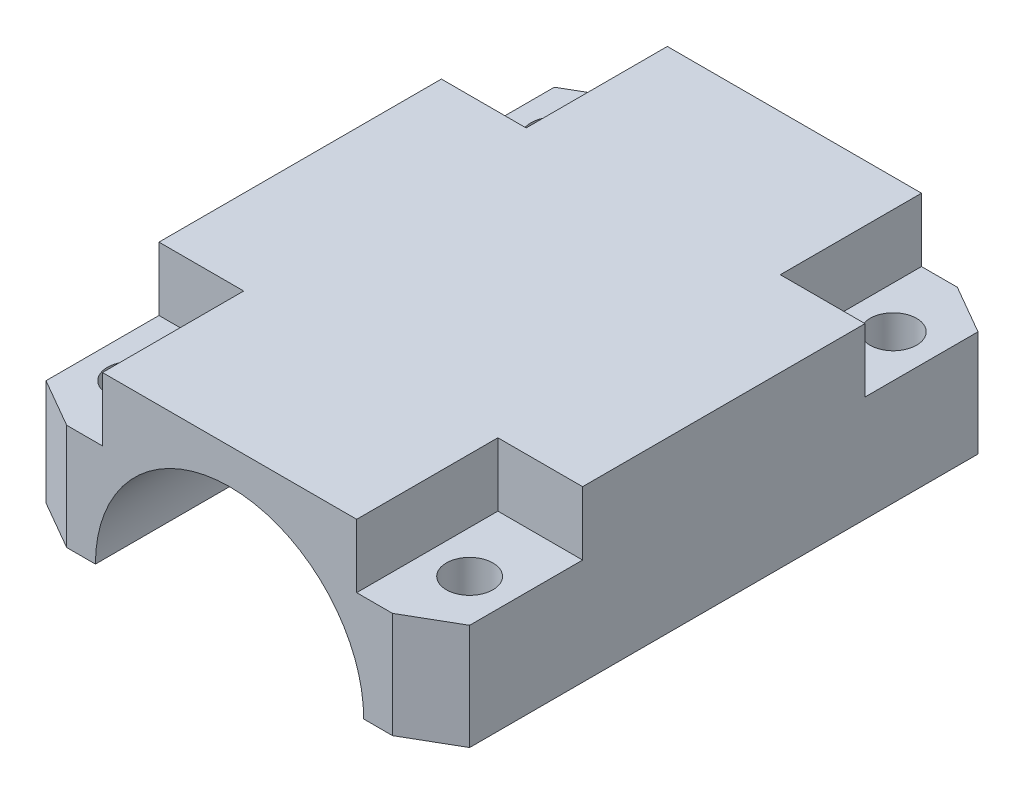
SolidWorks part; units mm, degrees
ref_plane "Plano frontal" through (0, 0, 0) normal (0, 0, 1) x (1, 0, 0)
ref_plane "Plano superior" through (0, 0, 0) normal (0, 1, 0) x (1, 0, 0)
ref_plane "Plano direito" through (0, 0, 0) normal (1, 0, 0) x (0, 0, -1)
sketch "Esboço1" plane through (0, 0, 0) normal (0, 1, 0) x (1, 0, 0)
  line L1 (0, 0) -> (-30, 0)
  line L2 (0, 0) -> (0, 40)
  line L3 (0, 40) -> (-30, 40)
  line L4 (-30, 0) -> (-30, 40)
  dimension "D1" = 30
  dimension "D2" = 40
extrude "Ressalto-extrusão1" add sketch "Esboço1" along normal blind 12
sketch "Esboço16" plane through (0, 0, 0) normal (0, -1, 0) x (1, 0, 0)
  line L1 (0, -40) -> (-30, -40) construction
  line L2 (-30, 0) -> (0, 0) construction
  line L4 (-15, -40) -> (-24.5, -40)
  line L5 (-15, -40) -> (-15, 0)
  line L6 (-15, 0) -> (-24.5, 0)
  line L7 (-24.5, -40) -> (-24.5, 0)
  point P1 (-15, -40)
  dimension "D1" = 9.5
revolve "Corte-Revolução1" cut sketch "Esboço16" angle 360 about L5
sketch "Esboço17" plane through (0, 0, 0) normal (0, -1, 0) x (1, 0, 0)
  line L0 (-23, -4) -> (-23, -36) construction
  line L1 (-27, -35) -> (-3, -35) construction
  line L2 (-27, -35) -> (-27, -5) construction
  line L3 (-27, -5) -> (-3, -5) construction
  line L4 (-3, -35) -> (-3, -5) construction
  line L5 (-5, 0) -> (-25, 0) construction
  line L6 (-30, -40) -> (-30, 0) construction
  line L8 (-24.5, -40) -> (-30, -40) construction
  circle A0 centre (-27, -35) radius 1.65
  circle A1 centre (-27, -5) radius 1.65
  circle A2 centre (-3, -35) radius 1.65
  circle A3 centre (-3, -5) radius 1.65
  point P8 (-27, -20)
  point P11 (-23, -20)
  point P12 (-15, -5)
  point P15 (-15, 0)
  dimension "D1" = 3.3
  dimension "D2" = 3
  dimension "D3" = 5
extrude "Corte-extrusão12" cut sketch "Esboço17" against normal through all
chamfer "Chanfro1" distance 2 angle 60 4 edges at (-30, 6, -40) (0, 6, -40) (-30, 6, 0) (0, 6, 0)
sketch "Esboço18" plane through (0, 12, 0) normal (0, 1, 0) x (1, 0, 0)
  line L0 (-6, 40) -> (-6, 30)
  line L1 (-3.4641, 40) -> (-26.5359, 40) construction
  line L2 (-6, 30) -> (0, 30)
  line L3 (0, 2) -> (0, 38) construction
  line L4 (0, 30) -> (0, 38)
  line L5 (0, 38) -> (-3.4641, 40)
  line L6 (-3.4641, 40) -> (-6, 40)
  line L7 (-24, 40) -> (-26.5359, 40)
  line L8 (-26.5359, 40) -> (-30, 38)
  line L9 (-30, 38) -> (-30, 30)
  line L10 (-30, 38) -> (-30, 2) construction
  line L11 (-30, 30) -> (-24, 30)
  line L12 (-24, 30) -> (-24, 40)
  line L13 (0, 10) -> (0, 2)
  line L14 (0, 2) -> (-3.4641, 0)
  line L15 (-26.5359, 0) -> (-3.4641, 0) construction
  line L16 (-3.4641, 0) -> (0, 2) construction
  line L17 (-3.4641, 0) -> (-6, 0)
  line L18 (-6, 0) -> (-6, 10)
  line L19 (-6, 10) -> (0, 10)
  line L20 (-24, 0) -> (-24, 10)
  line L21 (-24, 10) -> (-30, 10)
  line L22 (-30, 10) -> (-30, 2)
  line L23 (-30, 2) -> (-26.5359, 0)
  line L24 (-26.5359, 0) -> (-24, 0)
  dimension "D1" = 6
  dimension "D2" = 10
extrude "Corte-extrusão13" cut sketch "Esboço18" against normal blind 4.5
